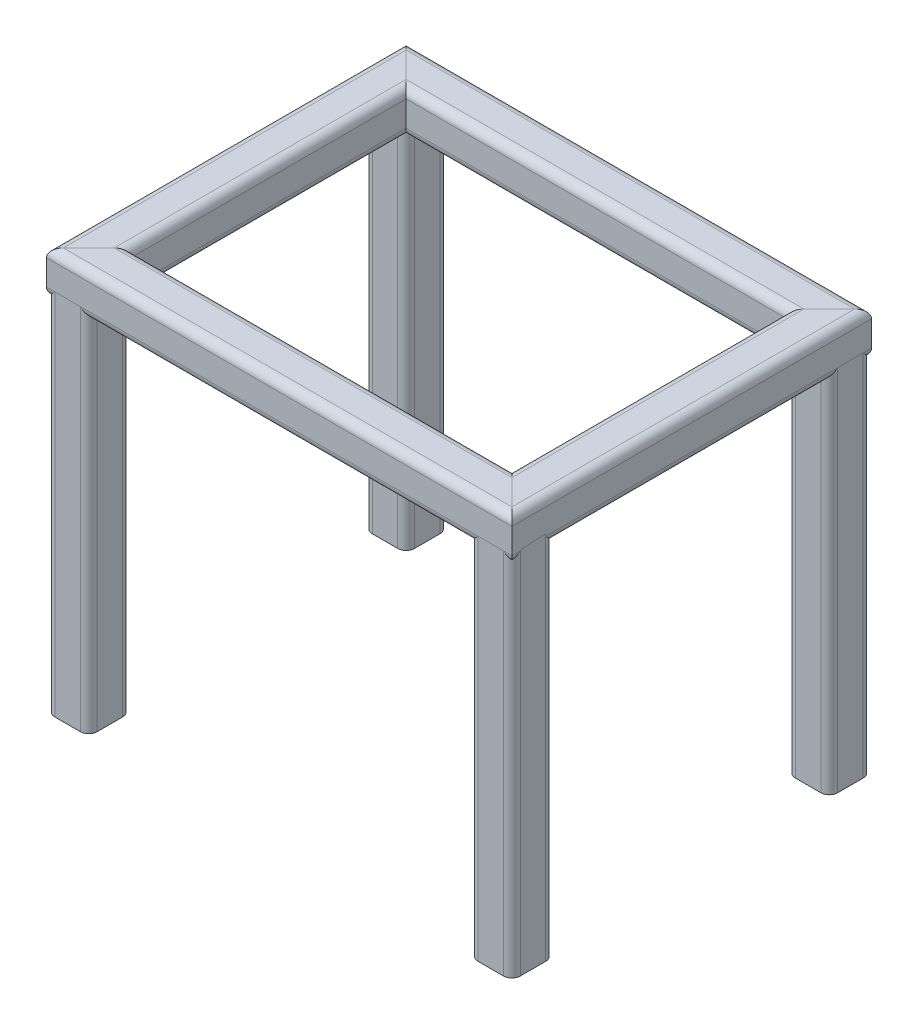
SolidWorks part; units mm, degrees
ref_plane "Front Plane" through (0, 0, 0) normal (0, 0, 1) x (1, 0, 0)
ref_plane "Top Plane" through (0, 0, 0) normal (0, 1, 0) x (1, 0, 0)
ref_plane "Right Plane" through (0, 0, 0) normal (1, 0, 0) x (0, 0, -1)
sketch3d "3DSketch1"
  line L0 (-100, 0, 75) -> (-100, -180, 75)
  line L1 (-100, 0, 75) -> (100, 0, 75)
  line L2 (-100, 0, 75) -> (-100, 0, -75)
  line L3 (-100, 0, -75) -> (100, 0, -75)
  line L4 (100, 0, 75) -> (100, 0, -75)
  line L5 (-100, 0, 75) -> (100, 0, -75) construction
  line L6 (-100, 0, -75) -> (100, 0, 75) construction
  line L7 (100, 0, 75) -> (100, -180, 75)
  line L8 (100, 0, -75) -> (100, -180, -75)
  line L9 (-100, 0, -75) -> (-100, -180, -75)
  point P1 (0, 0, 0)
  dimension "D1" = 200
  dimension "D2" = 150
  dimension "D3" = 180
other "Structural Member1"
ref_plane "Plane1" through (-100, 0, 75) normal (1, 0, 0) x (0, 0, -1)
sketch "Sketch1" plane through (-100, 0, 75) normal (1, 0, 0) x (0, 0, -1)
  line L0 (-6, -8) -> (6, -8)
  line L1 (-8, -6) -> (-8, 6)
  line L2 (6, 8) -> (-6, 8)
  line L3 (8, 6) -> (8, -6)
  line L4 (-6, -10) -> (6, -10)
  line L5 (-10, -6) -> (-10, 6)
  line L6 (6, 10) -> (-6, 10)
  line L7 (10, 6) -> (10, -6)
  arc A0 (10, 6) -> (6, 10) centre (6, 6) ccw
  arc A1 (6, -10) -> (10, -6) centre (6, -6) ccw
  arc A2 (-10, -6) -> (-6, -10) centre (-6, -6) ccw
  arc A3 (-6, 10) -> (-10, 6) centre (-6, 6) ccw
  arc A4 (-6, 8) -> (-8, 6) centre (-6, 6) ccw
  arc A5 (8, 6) -> (6, 8) centre (6, 6) ccw
  arc A6 (6, -8) -> (8, -6) centre (6, -6) ccw
  arc A7 (-8, -6) -> (-6, -8) centre (-6, -6) ccw
  point P0 (-10, 0)
  point P1 (10, 0)
  point P2 (0, 10)
  point P3 (0, -10)
  point P4 (0, 0)
  point P5 (-10, -10)
  point P6 (10, -10)
  point P7 (10, 10)
  point P8 (-10, 10)
  point P33 (0, 0)
  dimension "D1" = 4
  dimension "Thickness" = 2
  dimension "V_leg" = 20
other "Structural Member2"
ref_plane "Plane2" through (-100, 0, 75) normal (0, -1, 0) x (1, 0, 0)
sketch "Sketch17" plane through (-100, 0, 75) normal (0, -1, 0) x (1, 0, 0)
  line L0 (-6, -8) -> (6, -8)
  line L1 (-8, -6) -> (-8, 6)
  line L2 (6, 8) -> (-6, 8)
  line L3 (8, 6) -> (8, -6)
  line L4 (-6, -10) -> (6, -10)
  line L5 (-10, -6) -> (-10, 6)
  line L6 (6, 10) -> (-6, 10)
  line L7 (10, 6) -> (10, -6)
  arc A0 (10, 6) -> (6, 10) centre (6, 6) ccw
  arc A1 (6, -10) -> (10, -6) centre (6, -6) ccw
  arc A2 (-10, -6) -> (-6, -10) centre (-6, -6) ccw
  arc A3 (-6, 10) -> (-10, 6) centre (-6, 6) ccw
  arc A4 (-6, 8) -> (-8, 6) centre (-6, 6) ccw
  arc A5 (8, 6) -> (6, 8) centre (6, 6) ccw
  arc A6 (6, -8) -> (8, -6) centre (6, -6) ccw
  arc A7 (-8, -6) -> (-6, -8) centre (-6, -6) ccw
  point P0 (-10, 0)
  point P1 (10, 0)
  point P2 (0, 10)
  point P3 (0, -10)
  point P4 (0, 0)
  point P5 (-10, -10)
  point P6 (10, -10)
  point P7 (10, 10)
  point P8 (-10, 10)
  point P33 (0, 0)
  dimension "D1" = 4
  dimension "Thickness" = 2
  dimension "V_leg" = 20
